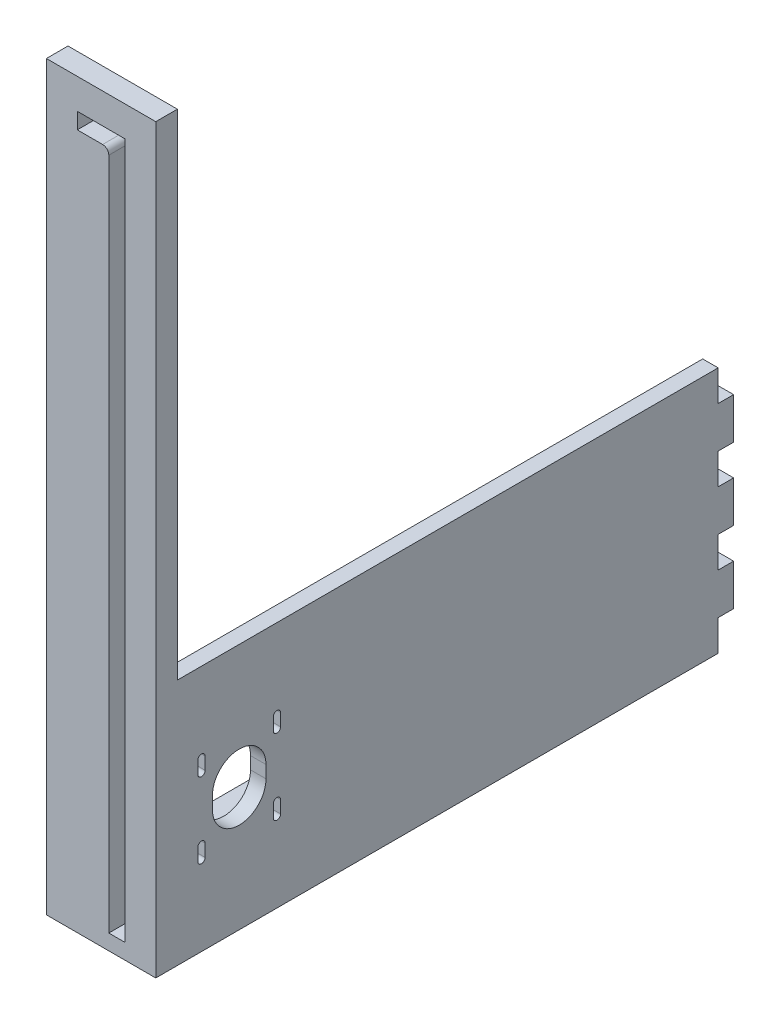
SolidWorks part; units mm, degrees
material "Acrylic (Medium-high impact)"
ref_plane "Front" through (0, 0, 0) normal (0, 0, 1) x (1, 0, 0)
ref_plane "Top" through (0, 0, 0) normal (0, 1, 0) x (1, 0, 0)
ref_plane "Right" through (0, 0, 0) normal (1, 0, 0) x (0, 0, -1)
sketch "Sketch1" plane through (0, 0, 0) normal (0, 0, 1) x (1, 0, 0)
  line L0 (0, 143.002) -> (0, -143.002) construction
  line L1 (-3.302, 133.858) -> (-3.302, -143.002)
  line L2 (-3.302, -143.002) -> (3.302, -143.002)
  line L3 (3.302, 143.002) -> (3.302, -143.002)
  line L4 (3.302, 143.002) -> (-16.256, 143.002)
  line L5 (-5.842, 136.398) -> (-16.256, 136.398)
  line L6 (-16.256, 143.002) -> (-16.256, 136.398)
  line L8 (-28.956, 155.448) -> (16.002, 155.448)
  line L9 (-28.956, 155.448) -> (-28.956, -149.352)
  line L10 (-28.956, -149.352) -> (16.002, -149.352)
  line L11 (16.002, 155.448) -> (16.002, -149.352)
  arc A0 (-3.302, 133.858) -> (-5.842, 136.398) centre (-5.842, 133.858) ccw
  point P2 (0, -143.002)
  point P11 (0, 0)
  dimension "D5" = 2.54
  dimension "D1" = 6.604
  dimension "D2" = 12.954
  dimension "D3" = 6.604
  dimension "D4" = 286.004
  dimension "D6" = 304.8
  dimension "D7" = 6.35
  dimension "D8" = 12.7
  dimension "D9" = 12.7
extrude "Boss-Extrude1" add sketch "Sketch1" along normal blind 8.89
sketch "Sketch2" plane through (16.002, 0, 0) normal (1, 0, 0) x (0, 0, -1)
  line L0 (-8.89, -149.352) -> (-8.89, 155.448) construction
  line L1 (-8.89, -47.752) -> (228.6, -47.752)
  line L2 (-8.89, -47.752) -> (-8.89, -149.352)
  line L3 (-8.89, -149.352) -> (228.6, -149.352)
  line L4 (228.6, -47.752) -> (228.6, -149.352)
  line L5 (14.4, -101.092) -> (14.4, -96.012)
  line L6 (36.4, -96.012) -> (36.4, -101.092)
  line L7 (8.4, -116.592) -> (8.4, -111.512)
  line L8 (11.4, -116.592) -> (11.4, -111.512)
  line L9 (8.4, -85.592) -> (8.4, -80.512)
  line L10 (11.4, -85.592) -> (11.4, -80.512)
  line L11 (25.4, -96.012) -> (25.4, -101.092) construction
  line L12 (42.4, -116.592) -> (42.4, -111.512)
  line L13 (39.4, -116.592) -> (39.4, -111.512)
  line L14 (39.4, -85.592) -> (39.4, -80.512)
  line L15 (42.4, -85.592) -> (42.4, -80.512)
  line L16 (0, -149.352) -> (0, 155.448) construction
  line L17 (225.425, -60.452) -> (225.425, -77.3853) construction
  line L18 (228.6, -47.752) -> (222.25, -47.752)
  line L19 (228.6, -47.752) -> (228.6, -60.452)
  line L20 (228.6, -60.452) -> (222.25, -60.452)
  line L21 (222.25, -47.752) -> (222.25, -60.452)
  line L22 (228.6, -107.0187) -> (222.25, -107.0187)
  line L23 (228.6, -107.0187) -> (228.6, -119.7187)
  line L24 (228.6, -119.7187) -> (222.25, -119.7187)
  line L25 (222.25, -107.0187) -> (222.25, -119.7187)
  line L26 (228.6, -136.652) -> (222.25, -136.652)
  line L27 (228.6, -136.652) -> (228.6, -149.352)
  line L28 (228.6, -149.352) -> (222.25, -149.352)
  line L29 (222.25, -136.652) -> (222.25, -149.352)
  line L30 (228.6, -77.3853) -> (222.25, -77.3853)
  line L31 (228.6, -77.3853) -> (228.6, -90.0853)
  line L32 (228.6, -90.0853) -> (222.25, -90.0853)
  line L33 (222.25, -77.3853) -> (222.25, -90.0853)
  line L34 (225.425, -90.0853) -> (225.425, -107.0187) construction
  line L35 (225.425, -119.7187) -> (225.425, -136.652) construction
  arc A0 (14.4, -101.092) -> (36.4, -101.092) centre (25.4, -101.092) ccw
  arc A1 (36.4, -96.012) -> (14.4, -96.012) centre (25.4, -96.012) ccw
  arc A2 (8.4, -116.592) -> (11.4, -116.592) centre (9.9, -116.592) ccw
  arc A3 (11.4, -111.512) -> (8.4, -111.512) centre (9.9, -111.512) ccw
  arc A4 (8.4, -85.592) -> (11.4, -85.592) centre (9.9, -85.592) ccw
  arc A5 (11.4, -80.512) -> (8.4, -80.512) centre (9.9, -80.512) ccw
  arc A6 (42.4, -116.592) -> (39.4, -116.592) centre (40.9, -116.592) cw
  arc A7 (39.4, -111.512) -> (42.4, -111.512) centre (40.9, -111.512) cw
  arc A8 (42.4, -85.592) -> (39.4, -85.592) centre (40.9, -85.592) cw
  arc A9 (39.4, -80.512) -> (42.4, -80.512) centre (40.9, -80.512) cw
  point P44 (25.4, -98.552)
  point P47 (-8.89, -98.552)
  line M17 (0, -149.352) -> (0, 155.448)
  line M19 (-8.89, 155.448) -> (-8.89, -149.352)
  line M20 (-8.89, -149.352) -> (0, -149.352)
  dimension "D1" = 22
  dimension "D6" = 1.5
  dimension "D10" = 1.5
  dimension "D2" = 5.08
  dimension "D3" = 5.08
  dimension "D4" = 15.5
  dimension "D5" = 15.5
  dimension "D7" = 15.5
  dimension "D8" = 15.5
  dimension "D9" = 5.08
  dimension "D11" = 25.4
  dimension "D12" = 50.8
  dimension "D13" = 203.2
  dimension "D14" = 12.7
  dimension "D15" = 6.35
extrude "Boss-Extrude2" add sketch "Sketch2" against normal blind 6.35 contours L33 L30 L4 L20 L21 L1 L3 L29 L26 L24 L25 L22 L32 A5 L10 A4 L9 A3 L8 A2 L7 A1 L6 A0 L5 L13 A7 L12 A6 L14 A9 L15 A8 M17 | L1 M19 M20 M17
sketch "Sketch3" plane through (9.652, 0, 0) normal (-1, 0, 0) x (0, 0, 1)
  line L0 (-222.25, -136.652) -> (-222.25, -149.352) construction
  line L1 (-222.25, -143.002) -> (0, -143.002)
  line L2 (-222.25, -143.002) -> (-222.25, -149.352)
  line L3 (-222.25, -149.352) -> (0, -149.352)
  line L4 (0, -143.002) -> (0, -149.352)
  point P4 (0, 0)
  dimension "D1" = 6.35
extrude "Boss-Extrude3" add sketch "Sketch3" along normal up to surface (38.608 mm away) up to face at (-28.956, 3.048, 4.445)
